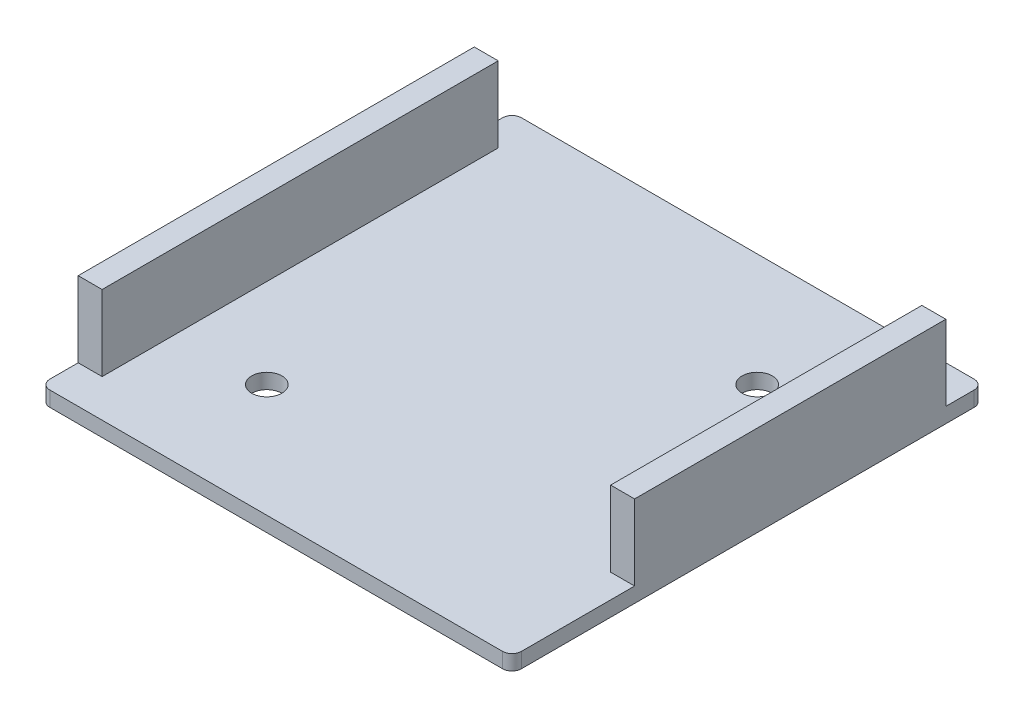
SolidWorks part; units mm, degrees
ref_plane "Front Plane" through (0, 0, 0) normal (0, 0, 1) x (1, 0, 0)
ref_plane "Top Plane" through (0, 0, 0) normal (0, 1, 0) x (1, 0, 0)
ref_plane "Right Plane" through (0, 0, 0) normal (1, 0, 0) x (0, 0, -1)
sketch "Sketch1" plane through (0, 0, 0) normal (0, 1, 0) x (1, 0, 0)
  line L1 (25, 25) -> (-25, 25)
  line L2 (25, 25) -> (25, -25)
  line L3 (25, -25) -> (-25, -25)
  line L4 (-25, 25) -> (-25, -25)
  line L5 (25, 25) -> (-25, -25) construction
  line L6 (25, -25) -> (-25, 25) construction
  point P0 (0, 0)
  dimension "D1" = 50
extrude "Boss-Extrude1" add sketch "Sketch1" along normal blind 1.6
sketch "Sketch2" plane through (0, 1.6, 0) normal (0, 1, 0) x (1, 0, 0)
  line L0 (-25.8341, -25.8341) -> (35329.505, 35329.505) construction
  line L1 (25, -25) -> (-35330.3391, 35330.3391) construction
  circle A0 centre (-13, -13) radius 1.6
  circle A1 centre (13, 13) radius 1.6
  dimension "D2" = 3.2
  dimension "D1" = 26
extrude "Cut-Extrude1" cut sketch "Sketch2" against normal through all
fillet "Fillet1" radius 1 4 edges at (25, 0.8, 25) (25, 0.8, -25) (-25, 0.8, -25) (-25, 0.8, 25)
sketch "Sketch3" plane through (0, 1.6, 0) normal (0, 1, 0) x (1, 0, 0)
  line L0 (0, 0) -> (50000, 0) construction
  line L1 (-25, 21) -> (-22.46, 21)
  line L2 (-25, 21) -> (-25, -21)
  line L3 (-25, -21) -> (-22.46, -21)
  line L4 (-22.46, 21) -> (-22.46, -21)
  line L5 (22.46, 21) -> (25, 21)
  line L6 (22.46, 21) -> (22.46, -12)
  line L7 (22.46, -12) -> (25, -12)
  line L8 (25, 21) -> (25, -12)
  line L9 (-25, 24) -> (-25, -24) construction
  line L10 (25, -24) -> (25, 24) construction
  dimension "D1" = 42
  dimension "D2" = 33
  dimension "D3" = 2.54
extrude "Boss-Extrude2" add sketch "Sketch3" along normal blind 8
